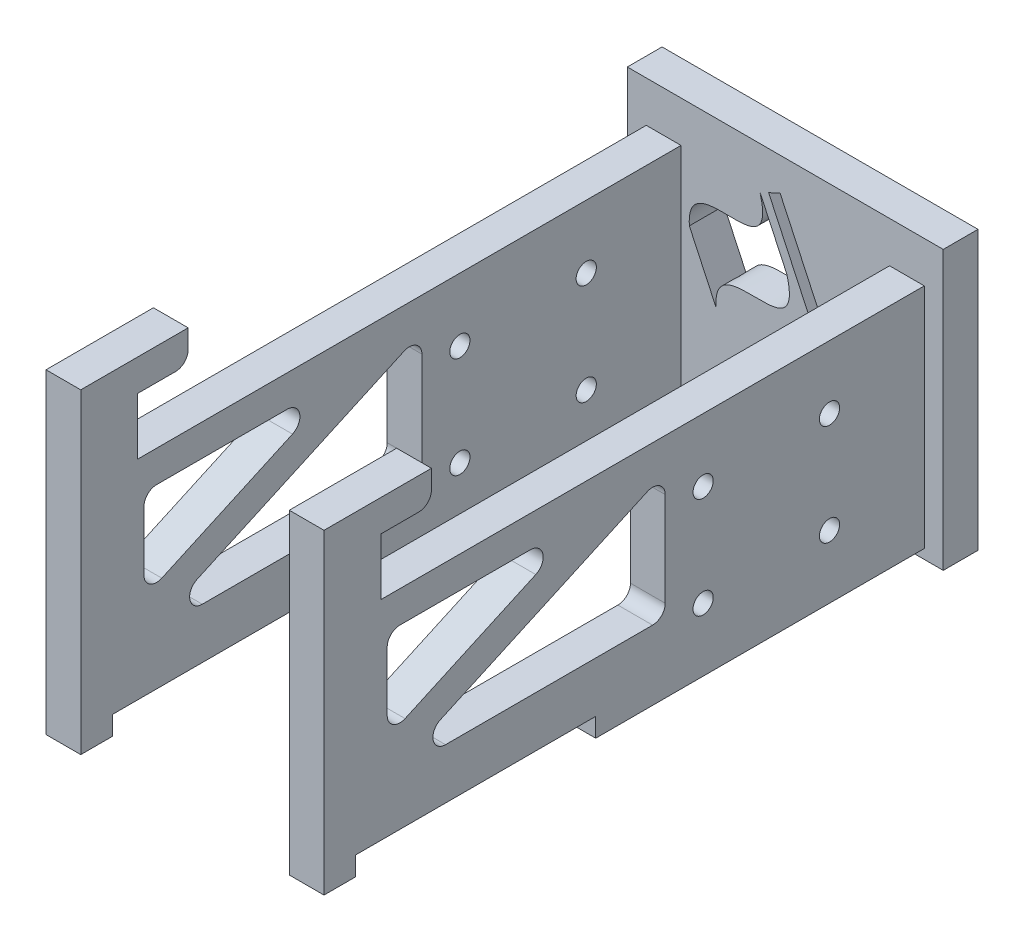
SolidWorks part; units mm, degrees
ref_plane "正面" through (0, 0, 0) normal (0, 0, 1) x (1, 0, 0)
ref_plane "平面" through (0, 0, 0) normal (0, 1, 0) x (1, 0, 0)
ref_plane "右側面" through (0, 0, 0) normal (1, 0, 0) x (0, 0, -1)
sketch "ｽｹｯﾁ1" plane through (0, 0, 0) normal (0, 0, 1) x (1, 0, 0)
  line L0 (-16.5, 20) -> (-16.5, -20) construction
  line L1 (25, -20) -> (-25, -20)
  line L2 (25, -20) -> (25, 20)
  line L3 (25, 20) -> (-25, 20)
  line L4 (-25, -20) -> (-25, 20)
  line L5 (25, -20) -> (-25, 20) construction
  line L6 (25, 20) -> (-25, -20) construction
  line L7 (16.5, 20) -> (16.5, -20) construction
  line L8 (0, -20) -> (0, 20) construction
  line L9 (-19.25, 0) -> (0, 0) construction
  line L10 (-16.5, 7.5) -> (-22, 7.5)
  line L11 (-16.5, 7.5) -> (-16.5, -7.5)
  line L12 (-16.5, -7.5) -> (-22, -7.5)
  line L13 (-22, 7.5) -> (-22, -7.5)
  line L14 (-16.5, 7.5) -> (-22, -7.5) construction
  line L15 (-16.5, -7.5) -> (-22, 7.5) construction
  line L16 (-19.25, -20) -> (-19.25, 20) construction
  line L17 (16.5, -7.5) -> (22, -7.5)
  line L18 (16.5, 7.5) -> (16.5, -7.5)
  line L19 (22, 7.5) -> (22, -7.5)
  line L20 (16.5, 7.5) -> (22, 7.5)
  line L21 (9.3262, -20) -> (-9.3262, 20) construction
  line L22 (-15.1842, 7.132) -> (-10.958, -1.9311)
  line L23 (-3.9937, 17.3233) -> (0.2325, 8.2602)
  line L24 (25, 11.6577) -> (-25, -11.6577) construction
  line L25 (-2.6357, 17.9565) -> (-0.8231, 18.8018)
  line L26 (-2.6357, 17.9565) -> (12.1559, -13.7643)
  line L27 (-0.8231, 18.8018) -> (13.9686, -12.919)
  line L28 (12.1559, -13.7643) -> (13.9686, -12.919)
  circle A0 centre (-19.25, 10.5) radius 1.6 construction
  circle A1 centre (-19.25, -10.5) radius 1.6 construction
  circle A2 centre (19.25, -10.5) radius 1.6 construction
  circle A3 centre (19.25, 10.5) radius 1.6 construction
  spline S0 degree 3 poles (-3.9937, 17.3233) (-0.9314, 6.2423) (-15.8296, 16.6385) (-15.1842, 7.132) knots 0 0 0 0 1 1 1 1
  spline S1 degree 3 poles (0.2325, 8.2602) (3.2948, -2.8208) (-11.6034, 7.5755) (-10.958, -1.9311) knots 0 0 0 0 1 1 1 1
  point P0 (0, 0)
  point P16 (-19.25, 0)
  point P21 (-19.25, 0)
  point P43 (0, 0)
  point P48 (0, 0)
  dimension "D9" = 3.2
  dimension "D1" = 33
  dimension "D2" = 16.5
  dimension "D3" = 40
  dimension "D4" = 50
  dimension "D5" = 5.5
  dimension "D6" = 15
  dimension "D7" = 3
  dimension "D8" = 3
  dimension "D10" = 25
  dimension "D11" = 2
  dimension "D12" = 1.4984
  dimension "D13" = 5.2
  dimension "D14" = 35
extrude "ﾎﾞｽ - 押し出し1" add sketch "ｽｹｯﾁ1" along normal blind 5.5
sketch "ｽｹｯﾁ2" plane through (-16.5, 0, 0) normal (-1, 0, 0) x (0, 0, 1)
  line L0 (0, 7.5) -> (5.5, 7.5)
  line L1 (5.5, 7.5) -> (5.5, 17.5)
  line L2 (5.5, 20) -> (5.5, -20) construction
  line L3 (5.5, 17.5) -> (100.5, 17.5)
  line L4 (100.5, 17.5) -> (100.5, -18.5)
  line L5 (100.5, -18.5) -> (5.5, -18.5)
  line L6 (5.5, -18.5) -> (5.5, -7.5)
  line L7 (5.5, -7.5) -> (0, -7.5)
  line L8 (0, 20) -> (0, -20) construction
  line L9 (5.5, -7.5) -> (0, -7.5) construction
  line L10 (0, -7.5) -> (0, 7.5)
  dimension "D1" = 10
  dimension "D2" = 11
  dimension "D3" = 95
extrude "ﾎﾞｽ - 押し出し2" add sketch "ｽｹｯﾁ2" along normal blind 5.5 separate body
sketch "ｽｹｯﾁ4" plane through (-22, 0, 0) normal (-1, 0, 0) x (0, 0, 1)
  line L0 (5.5, 17.5) -> (5.5, 7.5) construction
  line L1 (5.5, 20) -> (5.5, -20) construction
  line L2 (5.5, 7.5) -> (0, 7.5) construction
  line L3 (0, -7.5) -> (5.5, -7.5) construction
  circle A0 centre (5.5, 10.5) radius 0.5
  circle A1 centre (5.5, -10.5) radius 0.5
  dimension "D3" = 1
  dimension "D1" = 3
  dimension "D2" = 3
extrude "ｶｯﾄ - 押し出し1" [suppressed] cut sketch "ｽｹｯﾁ4" against normal through all
sketch "ｽｹｯﾁ5" plane through (0, 0, 5.5) normal (0, 0, -1) x (-1, 0, 0)
  point P0 (19.25, 10.5)
hole_wizard "Ø2.5 (2.5) 直径の穴1" [suppressed] positions "ｽｹｯﾁ5" profile "ｽｹｯﾁ7" hole size "Ø2.5" standard "JIS"
sketch "ｽｹｯﾁ7" plane through (-19.25, 10.5, 5.5) normal (1, 0, 0) x (0, 1, 0)
  line L0 (0, 0) -> (0, 10.7511)
  line L1 (0, 10.7511) -> (1.25, 10)
  line L2 (1.25, 10) -> (1.25, 0)
  line L5 (1.25, 0) -> (0, 0)
  line L10 (0, 10.7511) -> (-1.25, 10) construction
  line L11 (0, -6.35) -> (0, 107.95) construction
  dimension "穴の直径" = 2.5
  dimension "穴の深さ" = 10
  dimension "ﾄﾞﾘﾙ角度" = 118
sketch "ｽｹｯﾁ8" plane through (0, -18.5, 0) normal (0, -1, 0) x (1, 0, 0)
  line L0 (-22, 5.5) -> (-22, 100.5) construction
  line L1 (-16.5, 5.5) -> (-16.5, 100.5) construction
  line L2 (-22, 57.5) -> (-16.5, 57.5)
  line L3 (-22, 57.5) -> (-22, 95.5)
  line L4 (-22, 95.5) -> (-16.5, 95.5)
  line L5 (-16.5, 57.5) -> (-16.5, 95.5)
  line L6 (-22, 57.5) -> (-16.5, 95.5) construction
  line L7 (-22, 95.5) -> (-16.5, 57.5) construction
  line L8 (-22, 100.5) -> (-16.5, 100.5) construction
  point P6 (-19.25, 76.5)
  dimension "D1" = 38
  dimension "D2" = 5
extrude "ｶｯﾄ - 押し出し2" cut sketch "ｽｹｯﾁ8" against normal blind 3
sketch "ｽｹｯﾁ9" plane through (0, -15.5, 0) normal (0, -1, 0) x (-1, 0, 0)
  line L0 (19.25, -57.5) -> (19.25, -95.5) construction
  line L1 (22, -57.5) -> (16.5, -57.5) construction
  line L2 (16.5, -95.5) -> (22, -95.5) construction
  line L3 (16.5, -95.5) -> (22, -95.5) construction
  point P8 (19.25, -66.5)
  point P10 (19.25, -86.5)
  dimension "D1" = 9
  dimension "D2" = 9
hole_wizard "Ø2.5 (2.5) 直径の穴2" [suppressed] positions "ｽｹｯﾁ9" profile "ｽｹｯﾁ10" hole size "Ø2.5" standard "JIS"
sketch "ｽｹｯﾁ10" plane through (-19.25, -15.5, 86.5) normal (1, 0, 0) x (0, 0, -1)
  line L0 (0, 0) -> (0, 10.7511)
  line L1 (0, 10.7511) -> (1.25, 10)
  line L2 (1.25, 10) -> (1.25, 0)
  line L5 (1.25, 0) -> (0, 0)
  line L10 (0, 10.7511) -> (-1.25, 10) construction
  line L11 (0, -6.35) -> (0, 107.95) construction
  dimension "穴の直径" = 2.5
  dimension "穴の深さ" = 10
  dimension "ﾄﾞﾘﾙ角度" = 118
sketch "ｽｹｯﾁ11" plane through (-22, 0, 0) normal (-1, 0, 0) x (0, 0, 1)
  line L0 (95.5, -15.5) -> (57.5, -15.5) construction
  line L1 (95.5, -15.5) -> (95.5, -18.5) construction
  line L2 (57.5, -15.5) -> (57.5, -18.5) construction
  circle A0 centre (66.5, -15.5) radius 0.5
  circle A1 centre (86.5, -15.5) radius 0.5
  dimension "D1" = 1
  dimension "D2" = 9
  dimension "D3" = 9
extrude "ｶｯﾄ - 押し出し3" [suppressed] cut sketch "ｽｹｯﾁ11" against normal through all
hole_wizard "Ø2.5 (2.5) 直径の穴3" [suppressed] positions "ｽｹｯﾁ12" profile "ｽｹｯﾁ13" hole size "Ø2.5" standard "JIS"
sketch "ｽｹｯﾁ12" plane through (0, 17.5, 0) normal (0, 1, 0) x (1, 0, 0)
  line L0 (-19.25, -5.5) -> (-19.25, -100.5) construction
  line L1 (-22, -5.5) -> (-16.5, -5.5) construction
  line L3 (-22, -100.5) -> (-16.5, -100.5) construction
  point P10 (-19.25, -9.3)
  point P12 (-19.25, -96.5)
  dimension "D1" = 4
  dimension "D2" = 87.2
sketch "ｽｹｯﾁ13" plane through (-19.25, 17.5, 96.5) normal (1, 0, 0) x (0, 0, 1)
  line L0 (0, 0) -> (0, 10.7511)
  line L1 (0, 10.7511) -> (1.25, 10)
  line L2 (1.25, 10) -> (1.25, 0)
  line L5 (1.25, 0) -> (0, 0)
  line L10 (0, 10.7511) -> (-1.25, 10) construction
  line L11 (0, -6.35) -> (0, 107.95) construction
  dimension "穴の直径" = 2.5
  dimension "穴の深さ" = 10
  dimension "ﾄﾞﾘﾙ角度" = 118
sketch "ｽｹｯﾁ14" plane through (-22, 0, 0) normal (-1, 0, 0) x (0, 0, 1)
  line L0 (100.5, 17.5) -> (5.5, 17.5) construction
  line L1 (100.5, -18.5) -> (100.5, 17.5) construction
  circle A0 centre (9.3, 17.5) radius 1
  circle A1 centre (96.5, 17.5) radius 1
  dimension "D1" = 4
  dimension "D2" = 87.2
  dimension "D3" = 2
extrude "ｶｯﾄ - 押し出し4" [suppressed] cut sketch "ｽｹｯﾁ14" against normal through all
sketch "ｽｹｯﾁ16" plane through (0, 0, 100.5) normal (0, 0, 1) x (1, 0, 0)
  line L0 (-19.25, 17.5) -> (-19.25, -18.5) construction
  line L1 (-22, 17.5) -> (-16.5, 17.5) construction
  line L2 (-22, -18.5) -> (-16.5, -18.5) construction
  point P10 (-19.25, -13.5)
  point P12 (-19.25, 1.5)
  dimension "D1" = 5
  dimension "D2" = 20
hole_wizard "Ø2.5 (2.5) 直径の穴4" [suppressed] positions "ｽｹｯﾁ16" profile "ｽｹｯﾁ17" hole size "Ø2.5" standard "JIS"
sketch "ｽｹｯﾁ17" plane through (-19.25, 1.5, 100.5) normal (1, 0, 0) x (0, -1, 0)
  line L0 (0, 0) -> (0, 10.7511)
  line L1 (0, 10.7511) -> (1.25, 10)
  line L2 (1.25, 10) -> (1.25, 0)
  line L5 (1.25, 0) -> (0, 0)
  line L10 (0, 10.7511) -> (-1.25, 10) construction
  line L11 (0, -6.35) -> (0, 107.95) construction
  dimension "穴の直径" = 2.5
  dimension "穴の深さ" = 10
  dimension "ﾄﾞﾘﾙ角度" = 118
sketch "ｽｹｯﾁ18" plane through (-22, 0, 0) normal (-1, 0, 0) x (0, 0, 1)
  line L0 (100.5, -18.5) -> (100.5, 17.5) construction
  line L1 (95.5, -18.5) -> (100.5, -18.5) construction
  circle A0 centre (100.5, -13.5) radius 0.5
  circle A1 centre (100.5, 1.5) radius 0.5
  dimension "D1" = 1
  dimension "D2" = 1
  dimension "D3" = 5
  dimension "D4" = 20
extrude "ｶｯﾄ - 押し出し5" [suppressed] cut sketch "ｽｹｯﾁ18" against normal through all
sketch "ｽｹｯﾁ19" plane through (-22, 0, 0) normal (-1, 0, 0) x (0, 0, 1)
  line L0 (20.5, 17.5) -> (20.5, -18.5) construction
  line L1 (100.5, 17.5) -> (5.5, 17.5) construction
  line L2 (5.5, -18.5) -> (57.5, -18.5) construction
  line L3 (40.5, 17.5) -> (40.5, -18.5) construction
  line L4 (100.5, -18.5) -> (100.5, 17.5) construction
  line L5 (20.5, 7.5) -> (40.5, 7.5) construction
  line L6 (20.5, 7.5) -> (20.5, -8.5) construction
  line L7 (20.5, -8.5) -> (40.5, -8.5) construction
  line L8 (40.5, 7.5) -> (40.5, -8.5) construction
  line L9 (20.5, 7.5) -> (40.5, -8.5) construction
  line L10 (20.5, -8.5) -> (40.5, 7.5) construction
  line L11 (46.5, 9.394) -> (46.5, -5.5)
  line L12 (48.5, -7.5) -> (81.2668, -7.5)
  line L13 (82.0944, -3.6793) -> (49.3276, 11.2147)
  line L14 (67.8163, 12.5) -> (88.5, 12.5)
  line L15 (90.5, 10.5) -> (90.5, 1.0983)
  line L16 (87.6724, -0.7224) -> (66.9887, 8.6793)
  line L17 (100.5, -18.5) -> (100.5, 17.5) construction
  line L18 (95.5, -15.5) -> (57.5, -15.5) construction
  circle A0 centre (20.5, 7.5) radius 1.6
  circle A1 centre (20.5, -8.5) radius 1.6
  circle A2 centre (40.5, -8.5) radius 1.6
  circle A3 centre (40.5, 7.5) radius 1.6
  arc A4 (67.8163, 12.5) -> (66.9887, 8.6793) centre (67.8163, 10.5) ccw
  arc A5 (88.5, 12.5) -> (90.5, 10.5) centre (88.5, 10.5) cw
  arc A6 (90.5, 1.0983) -> (87.6724, -0.7224) centre (88.5, 1.0983) cw
  arc A7 (81.2668, -7.5) -> (82.0944, -3.6793) centre (81.2668, -5.5) ccw
  arc A8 (46.5, -5.5) -> (48.5, -7.5) centre (48.5, -5.5) ccw
  arc A9 (46.5, 9.394) -> (49.3276, 11.2147) centre (48.5, 9.394) cw
  point P13 (30.5, -0.5)
  point P37 (90.5, -7.5)
  point P42 (46.5, 12.5)
  dimension "D1" = 3.2
  dimension "D11" = 2
  dimension "D2" = 10
  dimension "D3" = 10
  dimension "D4" = 20
  dimension "D5" = 60
  dimension "D6" = 10
  dimension "D7" = 5
  dimension "D8" = 8
  dimension "D9" = 6
  dimension "D10" = 5
extrude "ｶｯﾄ - 押し出し6" cut sketch "ｽｹｯﾁ19" against normal through all
sketch "ｽｹｯﾁ20" plane through (-22, 0, 0) normal (-1, 0, 0) x (0, 0, 1)
  line L0 (91.5, 17.5) -> (91.5, 26.5)
  line L1 (100.5, 17.5) -> (5.5, 17.5) construction
  line L2 (91.5, 26.5) -> (85.5, 26.5)
  line L3 (83.5, 28.5) -> (83.5, 31.5)
  line L4 (83.5, 31.5) -> (100.5, 31.5)
  line L5 (100.5, 31.5) -> (100.5, 17.5)
  line L6 (5.5, 20) -> (5.5, -20) construction
  line L7 (91.5, 17.5) -> (100.5, 17.5)
  line L8 (100.5, -18.5) -> (100.5, 17.5) construction
  arc A0 (85.5, 26.5) -> (83.5, 28.5) centre (85.5, 28.5) cw
  dimension "D6" = 2
  dimension "D1" = 9
  dimension "D2" = 5
  dimension "D3" = 8
  dimension "D5" = 86
extrude "ﾎﾞｽ - 押し出し3" add sketch "ｽｹｯﾁ20" against normal up to surface (5.5 mm away) up to face at (-16.5, -8.5, 18.9)
mirror "ﾐﾗｰ1" about plane through (0, 0, 0) normal (1, 0, 0) of bodies 115 113
sketch "ｽｹｯﾁ21" plane through (0, 0, 0) normal (0, 0, -1) x (-1, 0, 0)
  line L0 (25, 20) -> (25, -20) construction
  line L1 (-25, 20) -> (25, 20)
  line L2 (-25, 20) -> (-25, 24)
  line L3 (-25, 24) -> (25, 24)
  line L4 (25, 20) -> (25, 24)
  line L5 (-25, 20) -> (25, 24) construction
  line L6 (-25, 24) -> (25, 20) construction
  point P4 (0, 22)
  dimension "D1" = 4
extrude "ﾎﾞｽ - 押し出し4" add sketch "ｽｹｯﾁ21" against normal up to surface (5.5 mm away) up to face at (0, 0, 5.5)
equation "\"D2@ｽｹｯﾁ1\"=\"D1@ｽｹｯﾁ1\"/2"
equation "\"D2@ｽｹｯﾁ12\"=84+3.2"
equation "\"D2@ｽｹｯﾁ14\"=84+3.2"
